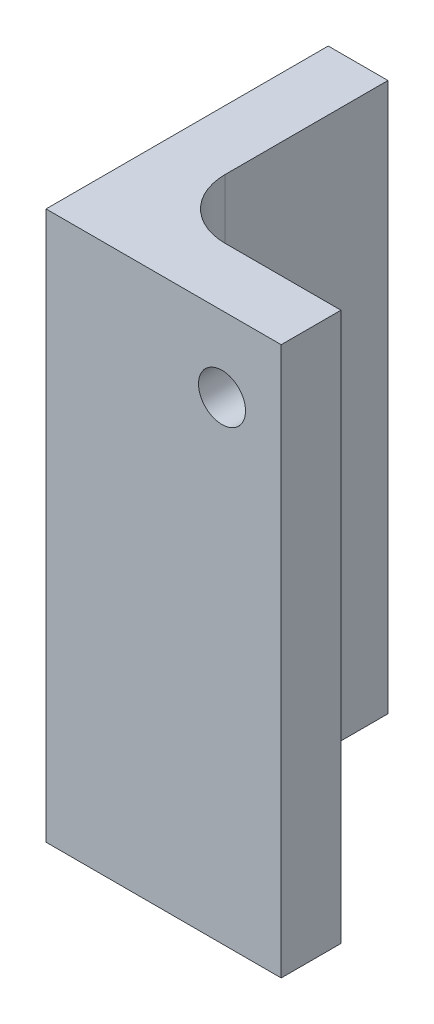
SolidWorks part; units mm, degrees
ref_plane "Front Plane" through (0, 0, 0) normal (0, 0, 1) x (1, 0, 0)
ref_plane "Top Plane" through (0, 0, 0) normal (0, 1, 0) x (1, 0, 0)
ref_plane "Right Plane" through (0, 0, 0) normal (1, 0, 0) x (0, 0, -1)
sketch "Sketch2" plane through (0, 0, 0) normal (0, 1, 0) x (1, 0, 0)
  line L0 (0, 0) -> (0, 30)
  line L1 (0, 30) -> (25, 30)
  line L2 (25, 30) -> (25, 23.65)
  line L3 (0, 0) -> (6.35, 0)
  line L4 (6.35, 0) -> (6.35, 17.3)
  line L5 (12.7, 23.65) -> (25, 23.65)
  arc A0 (6.35, 17.3) -> (12.7, 23.65) centre (12.7, 17.3) cw
  dimension "D4" = 6.35
  dimension "D1" = 6.35
  dimension "D2" = 6.35
  dimension "D3" = 30
  dimension "D5" = 25
extrude "Boss-Extrude1" add sketch "Sketch2" along normal blind 58.31
sketch "Sketch3" plane through (6.35, 0, 0) normal (1, 0, 0) x (0, 0, -1)
  line L1 (0, 10) -> (8.65, 10) construction
  line L3 (0, 58.31) -> (0, 0) construction
  line L4 (8.65, 10) -> (17.3, 10) construction
  line L5 (17.3, 58.31) -> (17.3, 0) construction
  line L6 (8.65, 10) -> (8.65, 30) construction
  line L7 (0, 0) -> (17.3, 0) construction
  circle A0 centre (8.65, 10) radius 2.5
  circle A1 centre (8.65, 30) radius 2.5
  dimension "D3" = 5
  dimension "D4" = 5
  dimension "D1" = 20
  dimension "D2" = 10
extrude "Cut-Extrude1" cut sketch "Sketch3" against normal through all
sketch "Sketch4" plane through (0, 0, -23.65) normal (0, 0, 1) x (1, 0, 0)
  line L0 (12.7, 0) -> (25, 0) construction
  circle A0 centre (18.7067, 50.31) radius 2.5
  dimension "D2" = 5
  dimension "D1" = 50.31
extrude "Cut-Extrude2" cut sketch "Sketch4" against normal through all
mirror "Mirror1" about plane through (0, 58.31, 0) normal (0, 0, -1) of "Cut-Extrude2", "Cut-Extrude1", "Boss-Extrude1"
sketch "Sketch5" plane through (0, 58.31, 0) normal (0, 1, 0) x (1, 0, 0)
  line L1 (25, 30) -> (0, 30)
  line L2 (25, 30) -> (25, 0)
  line L3 (25, 0) -> (0, 0)
  line L4 (0, 30) -> (0, 0)
extrude "Cut-Extrude3" cut sketch "Sketch5" against normal through all
